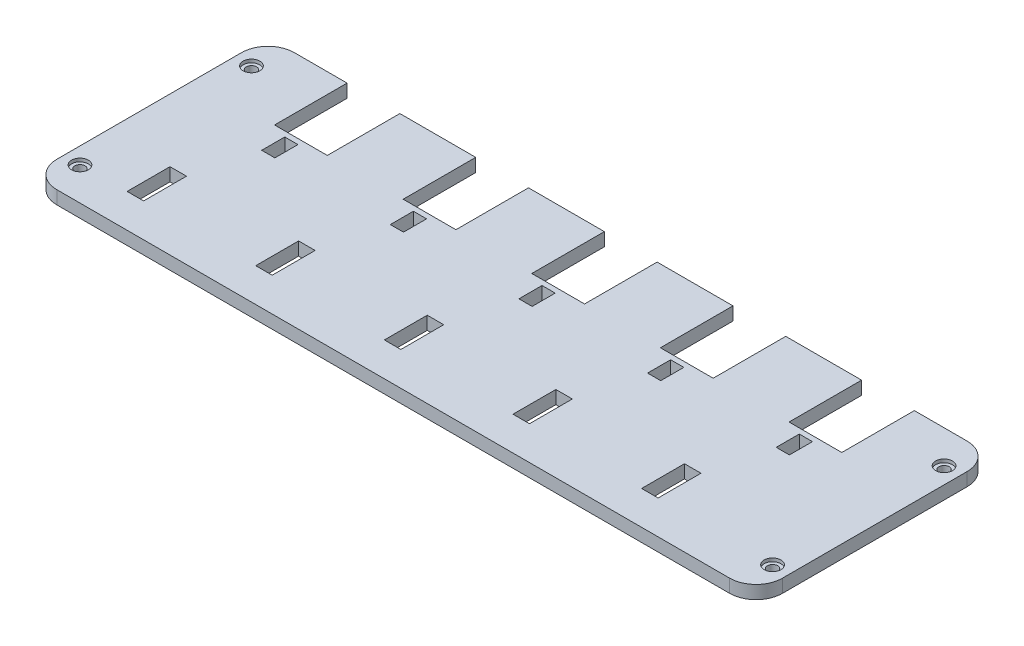
SolidWorks part; units mm, degrees
ref_plane "Спереди" through (0, 0, 0) normal (0, 0, 1) x (1, 0, 0)
ref_plane "Сверху" through (0, 0, 0) normal (0, 1, 0) x (1, 0, 0)
ref_plane "Справа" through (0, 0, 0) normal (1, 0, 0) x (0, 0, -1)
sketch "Sketch1" plane through (0, 0, 0) normal (0, 1, 0) x (1, 0, 0)
  line L0 (-0.2626, 9.171) -> (-0.2626, -1.829)
  line L1 (-34.5126, 9.171) -> (-27.2626, 9.171)
  line L3 (-34.5126, -26.829) -> (65.4874, -26.829)
  line L6 (-27.2626, 9.171) -> (-27.2626, -1.829)
  line L7 (-27.2626, -1.829) -> (-19.7626, -1.829)
  line L8 (-19.7626, 9.171) -> (-19.7626, -1.829)
  line L10 (-7.7626, 9.171) -> (-7.7626, -1.829)
  line L11 (-7.7626, -1.829) -> (-0.2626, -1.829)
  line L12 (19.2374, 9.171) -> (19.2374, -1.829)
  line L14 (11.7374, 9.171) -> (11.7374, -1.829)
  line L15 (11.7374, -1.829) -> (19.2374, -1.829)
  line L16 (38.7374, 9.171) -> (38.7374, -1.829)
  line L18 (31.2374, 9.171) -> (31.2374, -1.829)
  line L19 (31.2374, -1.829) -> (38.7374, -1.829)
  line L20 (58.2374, 9.171) -> (58.2374, -1.829)
  line L22 (50.7374, 9.171) -> (50.7374, -1.829)
  line L23 (50.7374, -1.829) -> (58.2374, -1.829)
  line L24 (-19.7626, 9.171) -> (-7.7626, 9.171)
  line L25 (-25.1626, -2.629) -> (-23.1626, -2.629)
  line L26 (-25.1626, -2.629) -> (-25.1626, -6.129)
  line L27 (-25.1626, -6.129) -> (-23.1626, -6.129)
  line L28 (-23.1626, -2.629) -> (-23.1626, -6.129)
  line L29 (-0.2626, 9.171) -> (11.7374, 9.171)
  line L30 (19.2374, 9.171) -> (31.2374, 9.171)
  line L31 (38.7374, 9.171) -> (50.7374, 9.171)
  line L32 (58.2374, 9.171) -> (65.4874, 9.171)
  line L33 (-5.6626, -2.629) -> (-3.6626, -2.629)
  line L34 (-3.6626, -2.629) -> (-3.6626, -6.129)
  line L35 (-5.6626, -6.129) -> (-3.6626, -6.129)
  line L36 (-5.6626, -2.629) -> (-5.6626, -6.129)
  line L37 (13.8374, -2.629) -> (15.8374, -2.629)
  line L38 (15.8374, -2.629) -> (15.8374, -6.129)
  line L39 (13.8374, -6.129) -> (15.8374, -6.129)
  line L40 (13.8374, -2.629) -> (13.8374, -6.129)
  line L41 (33.3374, -2.629) -> (35.3374, -2.629)
  line L42 (35.3374, -2.629) -> (35.3374, -6.129)
  line L43 (33.3374, -6.129) -> (35.3374, -6.129)
  line L44 (33.3374, -2.629) -> (33.3374, -6.129)
  line L45 (52.8374, -2.629) -> (54.8374, -2.629)
  line L46 (54.8374, -2.629) -> (54.8374, -6.129)
  line L47 (52.8374, -6.129) -> (54.8374, -6.129)
  line L48 (52.8374, -2.629) -> (52.8374, -6.129)
  line L49 (-10.4626, -15.229) -> (-7.9626, -15.229)
  line L50 (-29.9626, -15.229) -> (-27.4626, -15.229)
  line L51 (-29.9626, -15.229) -> (-29.9626, -21.729)
  line L52 (-29.9626, -21.729) -> (-27.4626, -21.729)
  line L53 (-27.4626, -15.229) -> (-27.4626, -21.729)
  line L54 (-10.4626, -15.229) -> (-10.4626, -21.729)
  line L55 (-7.9626, -15.229) -> (-7.9626, -21.729)
  line L56 (-10.4626, -21.729) -> (-7.9626, -21.729)
  line L57 (9.0374, -15.229) -> (11.5374, -15.229)
  line L58 (9.0374, -15.229) -> (9.0374, -21.729)
  line L59 (11.5374, -15.229) -> (11.5374, -21.729)
  line L60 (9.0374, -21.729) -> (11.5374, -21.729)
  line L61 (28.5374, -15.229) -> (31.0374, -15.229)
  line L62 (28.5374, -15.229) -> (28.5374, -21.729)
  line L63 (31.0374, -15.229) -> (31.0374, -21.729)
  line L64 (28.5374, -21.729) -> (31.0374, -21.729)
  line L65 (48.0374, -15.229) -> (50.5374, -15.229)
  line L66 (48.0374, -15.229) -> (48.0374, -21.729)
  line L67 (50.5374, -15.229) -> (50.5374, -21.729)
  line L68 (48.0374, -21.729) -> (50.5374, -21.729)
  line L70 (-34.5126, 9.171) -> (-35.5126, 9.171)
  line L72 (-34.5126, -26.829) -> (-35.5126, -26.829)
  line L73 (-39.5126, 5.171) -> (-39.5126, -22.829)
  line L74 (65.4874, 9.171) -> (66.4874, 9.171)
  line L76 (65.4874, -26.829) -> (66.4874, -26.829)
  line L77 (70.4874, 5.171) -> (70.4874, -22.829)
  circle A0 centre (-37.0126, 4.171) radius 0.775
  circle A1 centre (-37.0126, -21.829) radius 0.775
  circle A2 centre (67.9874, 4.171) radius 0.775
  circle A3 centre (67.9874, -21.829) radius 0.775
  arc A4 (66.4874, 9.171) -> (70.4874, 5.171) centre (66.4874, 5.171) cw
  arc A5 (66.4874, -26.829) -> (70.4874, -22.829) centre (66.4874, -22.829) ccw
  arc A6 (-35.5126, -26.829) -> (-39.5126, -22.829) centre (-35.5126, -22.829) cw
  arc A7 (-35.5126, 9.171) -> (-39.5126, 5.171) centre (-35.5126, 5.171) ccw
  point P9 (-24.1626, -2.629)
  point P49 (-28.7126, -15.229)
  point P93 (-39.5126, 9.171)
  dimension "D17" = 1.55
  dimension "D3" = 4
  dimension "D1" = 100
  dimension "D2" = 36
  dimension "D4" = 5
  dimension "D5" = 7.5
  dimension "D7" = 0.8
  dimension "D8" = 3.5
  dimension "D9" = 2
  dimension "D10" = 2.1
  dimension "D11" = 6.5
  dimension "D12" = 2.5
  dimension "D13" = 9.1
  dimension "D14" = 2.3
  dimension "D16" = 5
  dimension "D18" = 5
  dimension "D19" = 5
  dimension "D20" = 5
  dimension "D21" = 5
  dimension "D22" = 2.5
  dimension "D23" = 2.5
  dimension "D24" = 2.5
  dimension "D25" = 2.5
  dimension "D26" = 11
  dimension "D6" = 5
  dimension "D15" = 5
extrude "Boss-Extrude1" add sketch "Sketch1" along normal blind 2
sketch "Sketch2" plane through (0, 2, 0) normal (0, 1, 0) x (1, 0, 0)
  circle A0 centre (-37.0126, 4.171) radius 1.275
  circle A1 centre (-37.0126, -21.829) radius 1.275
  circle A2 centre (67.9874, 4.171) radius 1.275
  circle A3 centre (67.9874, -21.829) radius 1.275
  dimension "D1" = 2.55
extrude "Cut-Extrude1" cut sketch "Sketch2" against normal blind 0.5
sketch "Sketch3" plane through (0, 2, 0) normal (0, 1, 0) x (1, 0, 0)
  line L0 (-27.2626, 9.171) -> (-35.5126, 9.171) construction
  line L1 (-27.5126, 9.171) -> (-19.5126, 9.171)
  line L2 (-27.5126, 9.171) -> (-27.5126, -1.829)
  line L3 (-27.5126, -1.829) -> (-19.5126, -1.829)
  line L4 (-19.5126, 9.171) -> (-19.5126, -1.829)
  line L5 (-19.7626, -1.829) -> (-27.2626, -1.829) construction
  line L6 (-27.2626, -1.829) -> (-27.2626, 9.171) construction
  line L7 (-8.0126, 9.171) -> (-8.0126, -1.829)
  line L8 (-8.0126, -1.829) -> (-0.0126, -1.829)
  line L9 (-0.0126, 9.171) -> (-0.0126, -1.829)
  line L10 (-8.0126, 9.171) -> (-0.0126, 9.171)
  line L11 (11.4874, 9.171) -> (11.4874, -1.829)
  line L12 (11.4874, -1.829) -> (19.4874, -1.829)
  line L13 (19.4874, 9.171) -> (19.4874, -1.829)
  line L14 (11.4874, 9.171) -> (19.4874, 9.171)
  line L15 (30.9874, 9.171) -> (30.9874, -1.829)
  line L16 (30.9874, -1.829) -> (38.9874, -1.829)
  line L17 (38.9874, 9.171) -> (38.9874, -1.829)
  line L18 (30.9874, 9.171) -> (38.9874, 9.171)
  line L19 (50.4874, 9.171) -> (50.4874, -1.829)
  line L20 (50.4874, -1.829) -> (58.4874, -1.829)
  line L21 (58.4874, 9.171) -> (58.4874, -1.829)
  line L22 (50.4874, 9.171) -> (58.4874, 9.171)
  dimension "D1" = 8
  dimension "D2" = 0.25
  dimension "D3" = 5
extrude "Cut-Extrude2" cut sketch "Sketch3" against normal through all
